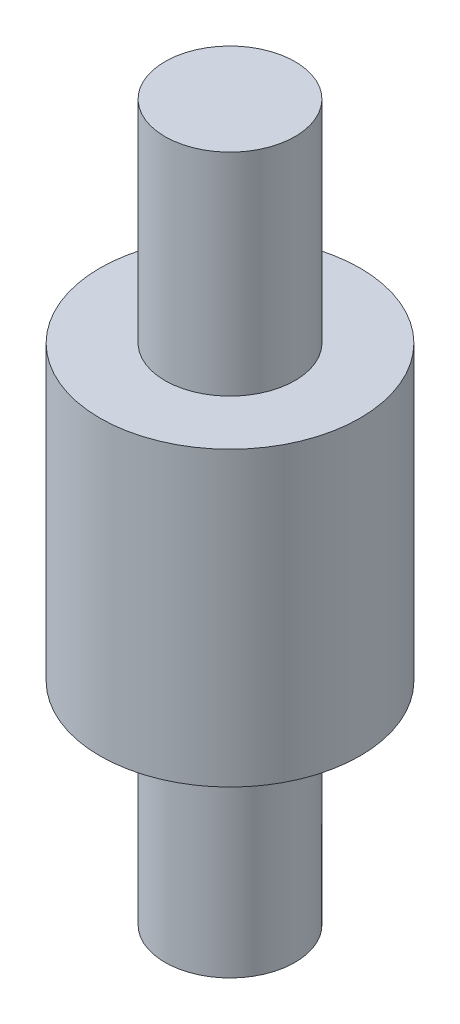
SolidWorks part; units mm, degrees
ref_plane "前视基准面" through (0, 0, 0) normal (0, 0, 1) x (1, 0, 0)
ref_plane "上视基准面" through (0, 0, 0) normal (0, 1, 0) x (1, 0, 0)
ref_plane "右视基准面" through (0, 0, 0) normal (1, 0, 0) x (0, 0, -1)
sketch "草图1" plane through (0, 0, 0) normal (0, 1, 0) x (1, 0, 0)
  circle A0 centre (0, 0) radius 8
extrude "凸台-拉伸1" add sketch "草图1" along normal blind 18
sketch "草图2" plane through (0, 18, 0) normal (0, 1, 0) x (1, 0, 0)
  circle A0 centre (0, 0) radius 4
extrude "凸台-拉伸2" add sketch "草图2" along normal blind 13
sketch "草图3" plane through (0, 0, 0) normal (0, -1, 0) x (1, 0, 0)
  circle A0 centre (0, 0) radius 4
extrude "凸台-拉伸3" add sketch "草图3" along normal blind 13
